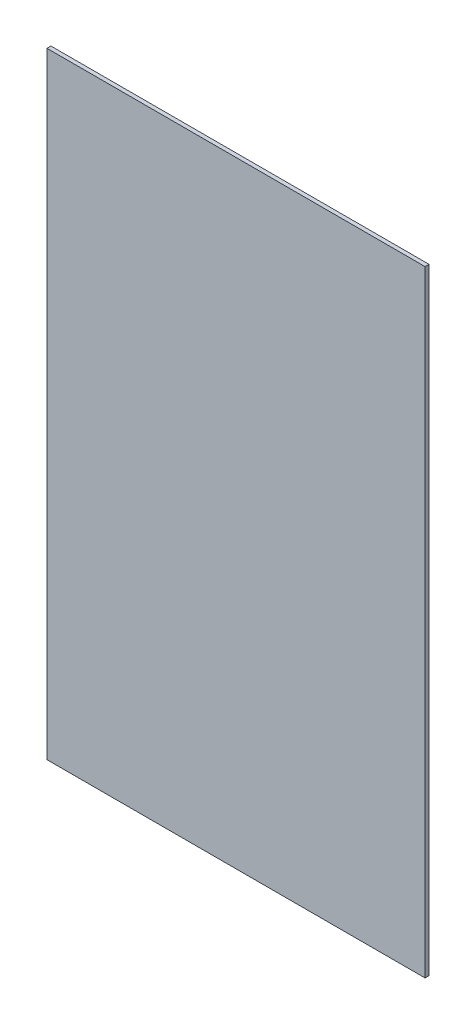
SolidWorks part; units mm, degrees
ref_plane "Plan de face" through (0, 0, 0) normal (0, 0, 1) x (1, 0, 0)
ref_plane "Plan de dessus" through (0, 0, 0) normal (0, 1, 0) x (1, 0, 0)
ref_plane "Plan de droite" through (0, 0, 0) normal (1, 0, 0) x (0, 0, -1)
sketch "Esquisse1" plane through (0, 0, 0) normal (0, 0, 1) x (1, 0, 0)
  line L1 (-67.5541, 66.6563) -> (218.4459, 66.6563)
  line L2 (-67.5541, 66.6563) -> (-67.5541, -399.3437)
  line L3 (-67.5541, -399.3437) -> (218.4459, -399.3437)
  line L4 (218.4459, 66.6563) -> (218.4459, -399.3437)
  dimension "D1" = 286
  dimension "D2" = 466
extrude "Boss.-Extru.1" add sketch "Esquisse1" along normal blind 3
equation "\"EpaisseurPlaque\"= 3"
equation "\"D1@Boss.-Extru.1\"=\"EpaisseurPlaque\""
equation "\"ProfondeurBoite\"=460"
equation "\"LongueurSyphon\"=270"
equation "\"LargeurSyphon\"=120"
equation "\"HauteurCoteDroit\"= 490"
equation "\"HauteurCoteGauche\"= 540"
equation "\"HauteurSolSyphon\"= 300"
equation "\"HauteurSyphon\"=\"HauteurCoteGauche\"-\"HauteurSolSyphon\""
equation "\"LargeurBoite\"= \"LargeurDroite\" + \"LargeurGauche\" + \"LargeurSyphon\""
equation "\"D2@Esquisse1\"=\"ProfondeurBoite\" + 2 * \"EpaisseurPlaque\""
equation "\"D1@Esquisse1\"=\"LargeurBoite\" + 2 * \"EpaisseurPlaque\""
equation "\"LargeurDroite\"=10"
equation "\"LargeurGauche\"=150"
